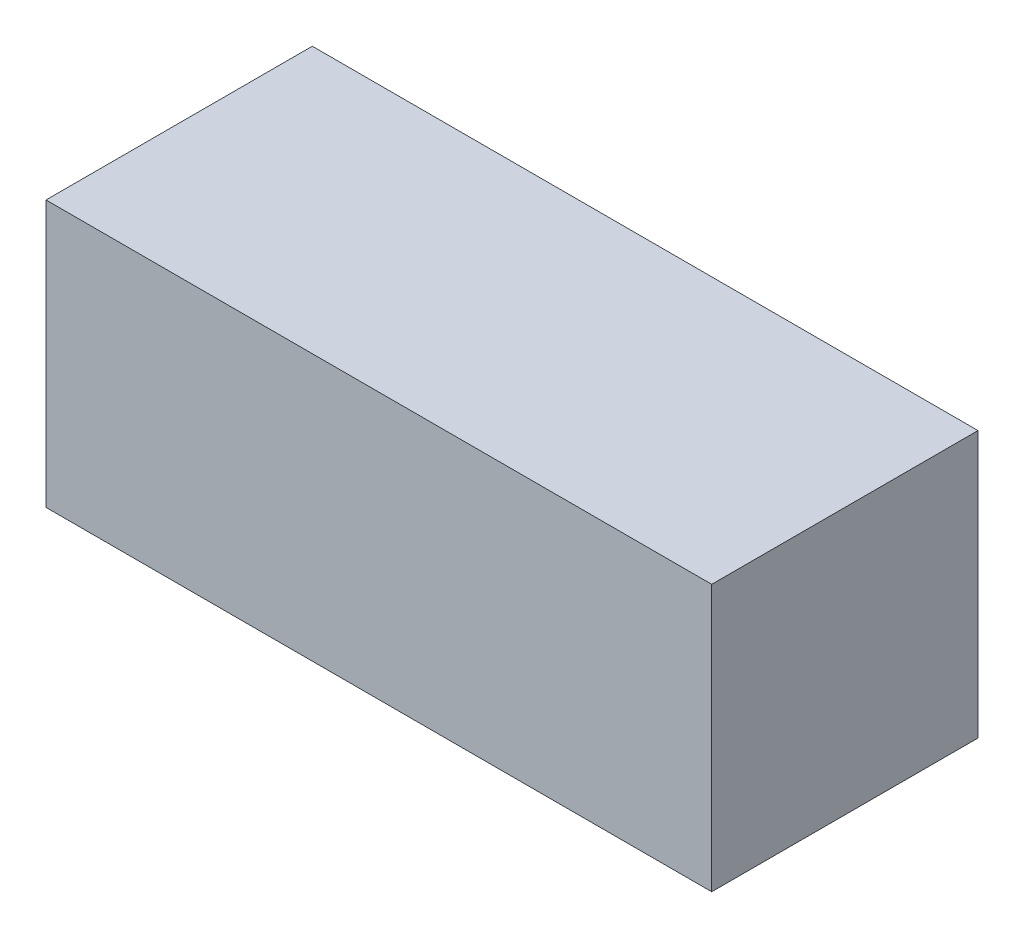
SolidWorks part; units mm, degrees
ref_plane "Front Plane" through (0, 0, 0) normal (0, 0, 1) x (1, 0, 0)
ref_plane "Top Plane" through (0, 0, 0) normal (0, 1, 0) x (1, 0, 0)
ref_plane "Right Plane" through (0, 0, 0) normal (1, 0, 0) x (0, 0, -1)
sketch "Sketch1" plane through (0, 0, 0) normal (0, 1, 0) x (1, 0, 0)
  line L1 (0, 0) -> (63.5, 0)
  line L2 (0, 0) -> (0, 25.4)
  line L3 (0, 25.4) -> (63.5, 25.4)
  line L4 (63.5, 0) -> (63.5, 25.4)
  dimension "D1" = 63.5
  dimension "D2" = 25.4
extrude "Boss-Extrude1" add sketch "Sketch1" along normal blind 25.4
